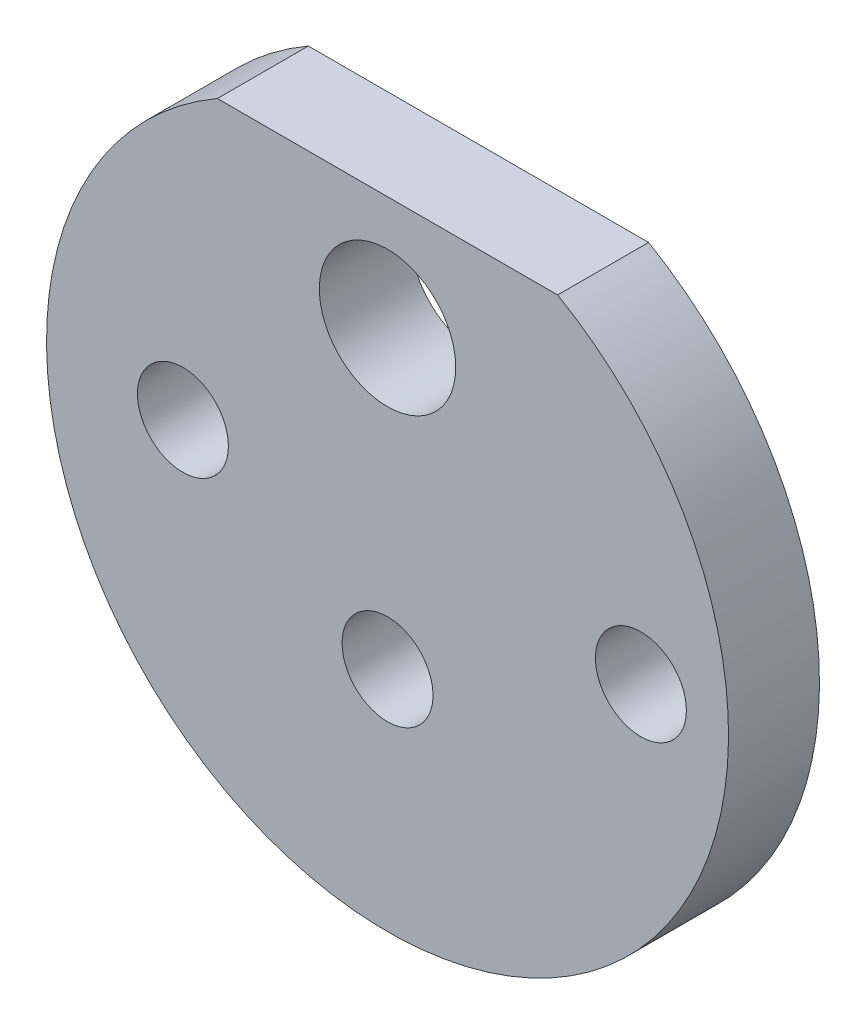
SolidWorks part; units mm, degrees
ref_plane "Front Plane" through (0, 0, 0) normal (0, 0, 1) x (1, 0, 0)
ref_plane "Top Plane" through (0, 0, 0) normal (0, 1, 0) x (1, 0, 0)
ref_plane "Right Plane" through (0, 0, 0) normal (1, 0, 0) x (0, 0, -1)
sketch "Sketch1" plane through (0, 0, 0) normal (0, 0, 1) x (1, 0, 0)
  line L0 (-7.4833, 13) -> (7.4833, 13)
  line L1 (0, 0) -> (0, 10.8978) construction
  line L2 (0, 0) -> (-10.5733, 0) construction
  arc A0 (-7.4833, 13) -> (7.4833, 13) centre (0, 0) ccw
  circle A1 centre (0, 8) radius 3
  circle A2 centre (-9, 0) radius 2
  circle A3 centre (11.1449, 0) radius 2
  dimension "D1" = 13
  dimension "D2" = 8
  dimension "D3" = 4
  dimension "D4" = 9
  dimension "D5" = 8
extrude "Boss-Extrude1" add sketch "Sketch1" along normal blind 4
sketch "Sketch2" plane through (0, 0, 0) normal (0, 0, -1) x (-1, 0, 0)
  circle A0 centre (0, -5) radius 6
  dimension "D2" = 12
  dimension "D1" = 5
extrude "Boss-Extrude2" add sketch "Sketch2" along normal blind 4
sketch "Sketch3" plane through (0, 0, -4) normal (0, 0, -1) x (-1, 0, 0)
  circle A0 centre (0, -5) radius 2
extrude "Cut-Extrude1" cut sketch "Sketch3" against normal through all
chamfer "Chamfer1" distance 0.5 angle 45 1 edges at (-6, -5, -4)
